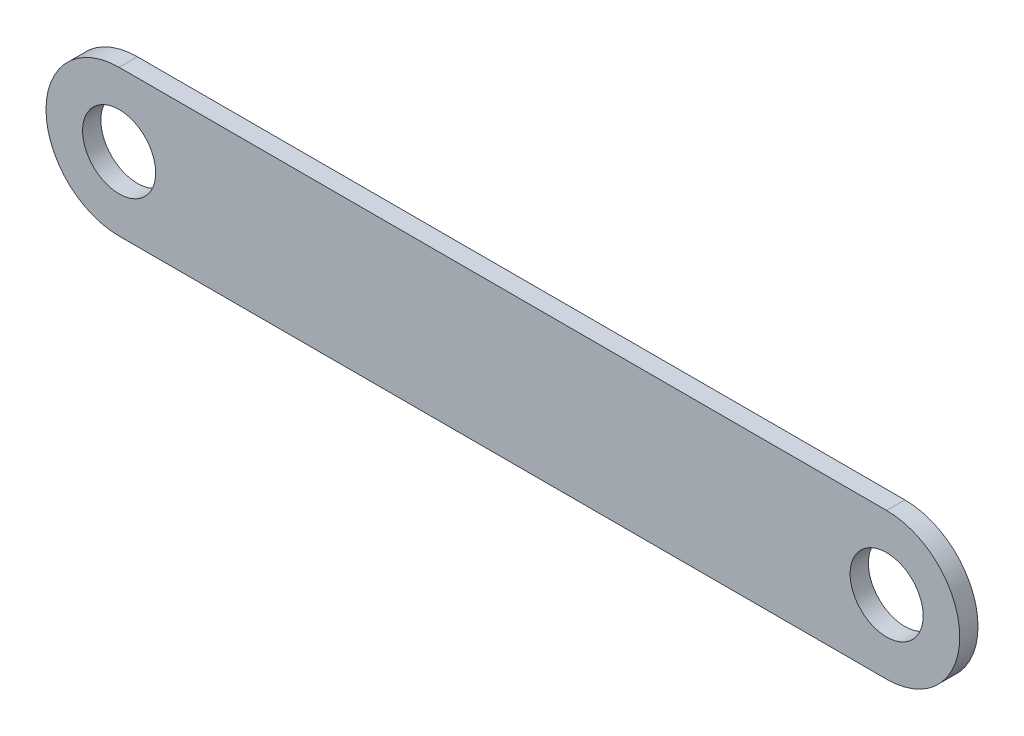
SolidWorks part; units mm, degrees
material "Pure Lead"
ref_plane "Front Plane" through (0, 0, 0) normal (0, 0, 1) x (1, 0, 0)
ref_plane "Top Plane" through (0, 0, 0) normal (0, 1, 0) x (1, 0, 0)
ref_plane "Right Plane" through (0, 0, 0) normal (1, 0, 0) x (0, 0, -1)
sketch "Sketch1" plane through (0, 0, 0) normal (0, 0, 1) x (1, 0, 0)
  line L0 (51.5131, 21.5571) -> (-158.4869, 21.5571)
  line L1 (-158.4869, -18.4429) -> (51.5131, -18.4429)
  arc A0 (51.5131, -18.4429) -> (51.5131, 21.5571) centre (51.5131, 1.5571) ccw
  arc A1 (-158.4869, 21.5571) -> (-158.4869, -18.4429) centre (-158.4869, 1.5571) ccw
  dimension "D2" = 20
  dimension "D1" = 210
extrude "Extrude1" add sketch "Sketch1" along normal blind 5
sketch "Sketch2" plane through (0, 0, 5) normal (0, 0, 1) x (1, 0, 0)
  circle A0 centre (-158.4869, 1.5571) radius 10
  circle A1 centre (51.5131, 1.5571) radius 10
  dimension "D1" = 20
extrude "Cut-Extrude1" cut sketch "Sketch2" against normal through all
